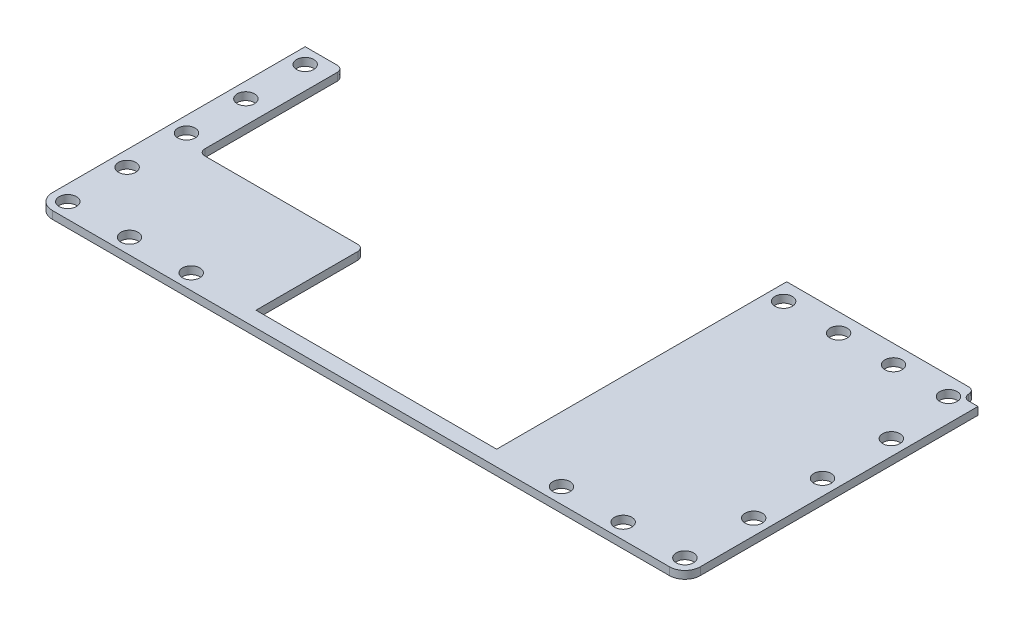
SolidWorks part; units mm, degrees
material "Zoltek Panex 33"
ref_plane "Front Plane" through (0, 0, 0) normal (0, 0, 1) x (1, 0, 0)
ref_plane "Top Plane" through (0, 0, 0) normal (0, 1, 0) x (1, 0, 0)
ref_plane "Right Plane" through (0, 0, 0) normal (1, 0, 0) x (0, 0, -1)
other "Bounding Box"
ref_plane "Default Plane" through (-8.9266, -12.7485, 0) normal (-0.1736, 0.9848, 0) x (0.9848, 0.1736, 0)
sketch "Sketch1" plane through (0, 0, 0) normal (0, 1, 0) x (1, 0, 0)
  line B0 (-66.675, 3.175) -> (-66.675, 55.2094)
  line B1 (-66.675, 55.2094) -> (-58.801, 55.2094)
  line B2 (-58.801, 55.2094) -> (-58.801, 36.83)
  line B3 (-58.801, 36.83) -> (-24.765, 36.83)
  line B4 (-24.765, 36.83) -> (-24.765, 3.175)
  line B5 (-24.765, 3.175) -> (24.765, 3.175)
  line B6 (24.765, 3.175) -> (24.765, 62.865)
  line B7 (24.765, 62.865) -> (62.23, 62.865)
  line B8 (-63.5, 0) -> (63.5, 0)
  line B9 (64.77, 60.325) -> (66.675, 60.325)
  line B10 (66.675, 60.325) -> (66.675, 3.175)
  arc B11 (66.675, 3.175) -> (63.5, 0) centre (63.5, 3.175) cw
  arc B12 (-63.5, 0) -> (-66.675, 3.175) centre (-63.5, 3.175) cw
  arc B13 (62.23, 62.865) -> (63.5, 61.595) centre (62.23, 61.595) cw
  arc B14 (63.5, 61.595) -> (64.77, 60.325) centre (64.77, 61.595) ccw
sketch_block_instance "Center Top plate-1"
sketch_block "Center Top plate" parameters "D3"=3.175, "D4"=3.175, "D1"=36.83, "D2"=7.874
extrude "Boss-Extrude1" add sketch "Sketch1" along normal blind 1.5875
sketch "Sketch2" plane through (0, 1.5875, 0) normal (0, 1, 0) x (-1, 0, 0)
  line L0 (66.675, -3.175) -> (-66.675, -3.175) construction
  line L2 (63.5, 0) -> (-63.5, 0) construction
  line L3 (63.5, -3.175) -> (63.5, -55.2094) construction
  line L4 (58.801, -55.2094) -> (66.675, -55.2094) construction
  line L5 (-63.5, -3.175) -> (-63.5, -57.6871) construction
  line L6 (-63.5, -57.6871) -> (-61.8697, -59.055) construction
  line L7 (-61.8697, -59.055) -> (-27.94, -59.055) construction
  line L8 (-27.94, -59.055) -> (-27.94, -6.35) construction
  line L10 (-62.23, -62.865) -> (-24.765, -62.865) construction
  line L11 (-24.765, -62.865) -> (-24.765, -3.175) construction
  arc A0 (66.675, -3.175) -> (63.5, 0) centre (63.5, -3.175) ccw construction
  arc A1 (-63.5, 0) -> (-66.675, -3.175) centre (-63.5, -3.175) ccw construction
  circle A2 centre (63.5, -3.175) radius 1.778
  circle A3 centre (50.8, -3.175) radius 1.778
  circle A4 centre (38.1, -3.175) radius 1.778
  circle A10 centre (-38.1, -3.175) radius 1.778
  circle A11 centre (-50.8, -3.175) radius 1.778
  circle A12 centre (-63.5, -3.175) radius 1.778
  circle A13 centre (63.5, -15.3898) radius 1.778
  circle A14 centre (63.5, -27.6047) radius 1.778
  circle A15 centre (63.5, -39.8195) radius 1.778
  circle A16 centre (63.5, -52.0344) radius 1.778
  arc A17 (-63.5, -61.595) -> (-64.77, -60.325) centre (-64.77, -61.595) ccw construction
  circle A18 centre (-63.5, -17.3376) radius 1.778
  circle A19 centre (-63.5, -31.5002) radius 1.778
  circle A20 centre (-63.5, -45.6628) radius 1.778
  circle A22 centre (-61.8697, -59.055) radius 1.778
  circle A23 centre (-50.5598, -59.055) radius 1.778
  circle A24 centre (-39.2499, -59.055) radius 1.778
  circle A25 centre (-27.94, -59.055) radius 1.778
  arc A30 (-23.622, -3.175) -> (-27.178, -3.175) centre (-25.4, -3.175) ccw [skipped]
  arc A31 (-13.5736, -4.7236) -> (-10.922, -3.175) centre (-12.7, -3.175) ccw [skipped]
  arc A32 (1.778, -3.175) -> (-1.778, -3.175) centre (0, -3.175) ccw [skipped]
  arc A33 (10.922, -3.175) -> (14.478, -3.175) centre (12.7, -3.175) ccw [skipped]
  arc A34 (27.178, -3.175) -> (23.622, -3.175) centre (25.4, -3.175) ccw [skipped]
  dimension "D2" = 3.556
  dimension "D12" = 3.556
  dimension "D1" = 3.175
  dimension "D3" = 3.175
  dimension "D5" = 3.175
  dimension "D6" = 5
  dimension "D7" = 3.175
  dimension "D8" = 3.81
  dimension "D9" = 3.175
  dimension "D10" = 3.81
  dimension "D11" = 130
  dimension "D16" = 3.175
  dimension "D17" = 14.1626
  dimension "D18" = 14.1626
  dimension "D19" = 14.1626
  dimension "D4" = 11
  dimension "D14" = 4
extrude "Cut-Extrude1" cut sketch "Sketch2" against normal through all both and the other way through all
fillet "Fillet1" radius 1.27 3 edges at (-24.765, 0.7937, -36.83) (-58.801, 0.7937, -36.83) (-58.801, 0.7937, -55.2094)
sketch "Sketch3" plane through (0, 1.5875, 0) normal (0, 1, 0) x (1, 0, 0)
  line L0 (-24.765, 3.175) -> (-24.765, 35.56) construction
  line L1 (-58.801, 38.1) -> (-24.765, 38.1)
  line L2 (-58.801, 38.1) -> (-58.801, 25.4)
  line L3 (-58.801, 25.4) -> (-24.765, 25.4)
  line L4 (-24.765, 38.1) -> (-24.765, 25.4)
  dimension "D1" = 12.7
extrude "Cut-Extrude2" cut sketch "Sketch3" against normal through all both and the other way through all
fillet "Fillet2" radius 1.27 2 edges at (-24.765, 0.7937, -25.4) (-58.801, 0.7937, -25.4)
